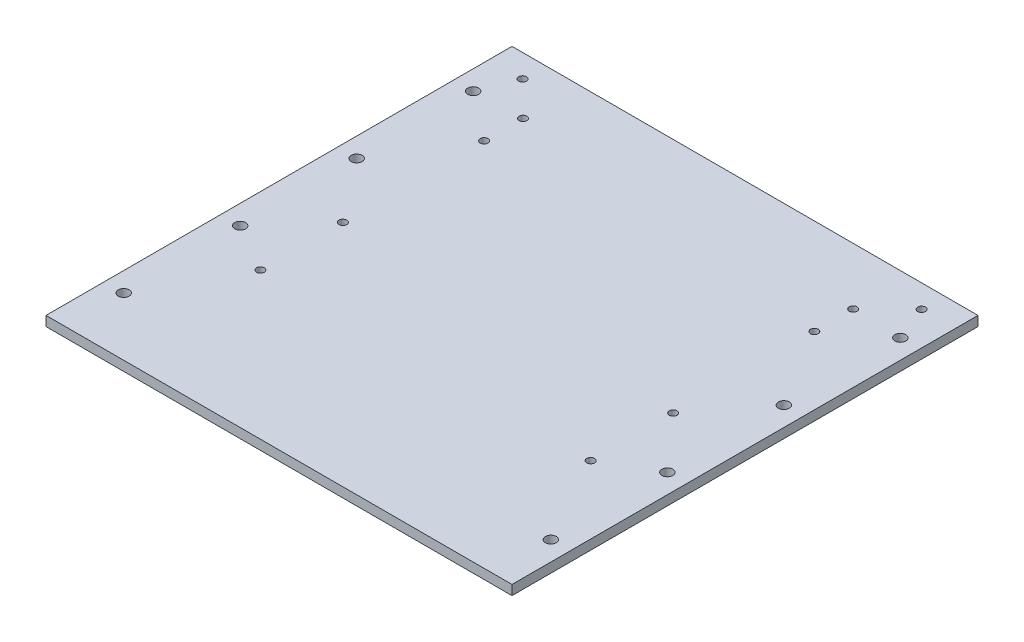
SolidWorks part; units mm, degrees
material "6061-T6 (SS)"
ref_plane "Front Plane" through (0, 0, 0) normal (0, 0, 1) x (1, 0, 0)
ref_plane "Top Plane" through (0, 0, 0) normal (0, 1, 0) x (1, 0, 0)
ref_plane "Right Plane" through (0, 0, 0) normal (1, 0, 0) x (0, 0, -1)
sketch "Sketch1" plane through (0, 0, 0) normal (0, 1, 0) x (1, 0, 0)
  line L0 (0, 152.4) -> (0, -152.4)
  line L1 (0, 152.4) -> (152.4, 152.4)
  line L3 (0, -152.4) -> (152.4, -152.4)
  line L4 (152.4, 152.4) -> (152.4, -152.4)
  dimension "D1" = 304.8
  dimension "D2" = 152.4
extrude "Boss-Extrude1" add sketch "Sketch1" along normal blind 6.35
hole_wizard "1/4-20 Tapped Hole1" positions "Sketch3" profile "Sketch2" tap size "1/4-20" standard "ANSI Inch" end condition through all
sketch "Sketch3" plane through (0, 6.35, 0) normal (0, 1, 0) x (1, 0, 0)
  line L0 (0, 152.4) -> (0, -152.4) construction
  line L1 (152.4, 152.4) -> (0, 152.4) construction
  line L2 (108, -2.6) -> (108, -56.575)
  line L4 (108, -29.5875) -> (0, -29.5875)
  line L5 (108, 115.175) -> (108, 89.775)
  point P0 (130.5, 137.4)
  point P2 (108, 115.175)
  point P9 (108, -2.6)
  point P11 (108, -56.575)
  point P22 (108, 89.775)
  dimension "D1" = 22.5
  dimension "D2" = 130.5
  dimension "D3" = 22.225
  dimension "D4" = 15
  dimension "D5" = 53.975
  dimension "D6" = 140
  dimension "D7" = 25.4
sketch "Sketch2" plane through (130.5, 6.35, -137.4) normal (1, 0, 0) x (0, 0, 1)
  line L0 (0, 0) -> (0, 6.35)
  line L1 (0, 6.35) -> (2.5527, 6.35)
  line L2 (2.5527, 6.35) -> (2.5527, 0)
  line L5 (2.5527, 0) -> (0, 0)
  line L11 (0, -6.35) -> (0, 107.95) construction
  dimension "Thru Tap Drill Dia." = 5.1054
  dimension "Thru Tap Drill Depth" = 6.35
cosmetic thread "Hole Thread1" parameters "D1"=6.35, "D2"=6.35
cosmetic thread "Hole Thread2" parameters "D1"=6.35, "D2"=6.35
cosmetic thread "Hole Thread4" parameters "D1"=6.35, "D2"=6.35
cosmetic thread "Hole Thread5" parameters "D1"=6.35, "D2"=6.35
cosmetic thread "Hole Thread6" parameters "D1"=6.35, "D2"=6.35
hole_wizard "1/4 Clearance Hole2" positions "Sketch5" profile "Sketch4" hole size "1/4" standard "ANSI Inch"
sketch "Sketch5" plane through (0, 6.35, 0) normal (0, 1, 0) x (1, 0, 0)
  line L6 (152.4, 152.4) -> (0, 152.4) construction
  line L10 (0, 152.4) -> (0, -152.4) construction
  point P0 (139.7, 114.3)
  dimension "D1" = 139.7
  dimension "D2" = 38.1
sketch "Sketch4" plane through (139.7, 6.35, -114.3) normal (1, 0, 0) x (0, 0, 1)
  line L0 (0, 0) -> (0, 14.8458)
  line L1 (0, 14.8458) -> (3.5712, 12.7)
  line L2 (3.5712, 12.7) -> (3.5712, 0)
  line L5 (3.5712, 0) -> (0, 0)
  line L10 (0, 14.8458) -> (-3.5712, 12.7) construction
  line L11 (0, -6.35) -> (0, 107.95) construction
  dimension "Hole Dia." = 7.1425
  dimension "Hole Depth" = 12.7
  dimension "Drill Angle" = 118
pattern_linear "LPattern1" count 4 spacing 76.2 along (0, 0, 1) of "1/4 Clearance Hole2"
mirror "Mirror1" about plane through (0, 0, 0) normal (1, 0, 0) of bodies 105 101
